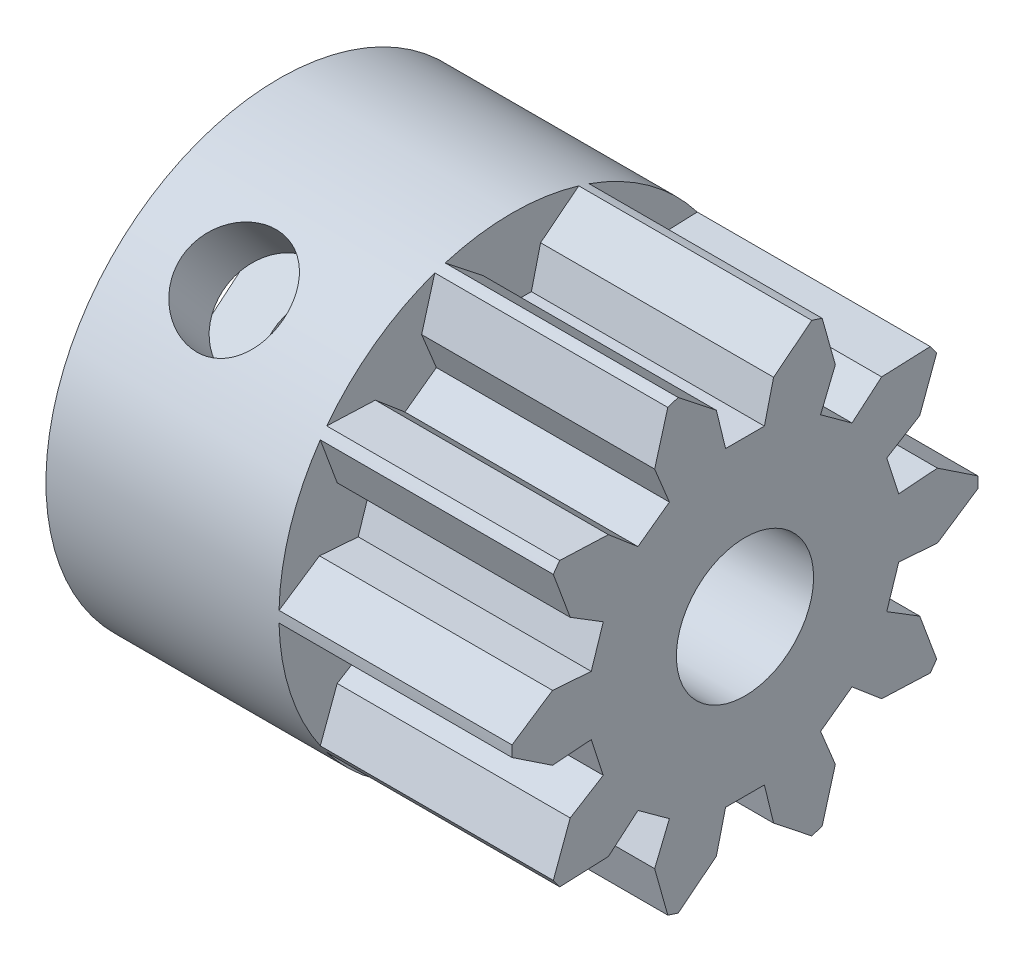
SolidWorks part; units mm, degrees
ref_plane "Plan de face" through (0, 0, 0) normal (0, 0, 1) x (1, 0, 0)
ref_plane "Plan de dessus" through (0, 0, 0) normal (0, 1, 0) x (1, 0, 0)
ref_plane "Plan de droite" through (0, 0, 0) normal (1, 0, 0) x (0, 0, -1)
sketch "Esquisse1" plane through (0, 0, 0) normal (1, 0, 0) x (0, 0, -1)
  circle A0 centre (0, 0) radius 9
  circle A1 centre (0, 0) radius 2.65
  dimension "D1" = 18
  dimension "D2" = 5.3
extrude "Boss.-Extru.1" add sketch "Esquisse1" along normal blind 18
sketch "Esquisse5" plane through (18, 0, 0) normal (1, 0, 0) x (0, 0, -1)
  line L0 (-0.75, 6) -> (0.75, 6)
  line L1 (0, 0) -> (0, 9) construction
  line L2 (-1.105, 7.4574) -> (1.105, 7.4574) construction
  line L3 (2.5796, 8.6224) -> (-2.5796, 8.6224) construction
  line L4 (-0.75, 6) -> (-1.105, 7.4574)
  line L5 (-1.105, 7.4574) -> (-2.5796, 8.6224)
  line L6 (0.75, 6) -> (1.105, 7.4574)
  line L7 (1.105, 7.4574) -> (2.5796, 8.6224)
  circle A0 centre (0, 0) radius 9 construction
  arc A1 (-2.5796, 8.6224) -> (2.5796, 8.6224) centre (0, 0) cw
  point P8 (0, 6)
  dimension "D1" = 1.5
  dimension "D2" = 3
  dimension "D3" = 1.5
  dimension "D4" = 142
  dimension "D5" = 2.21
extrude "Enlèv. mat.-Extru.2" cut sketch "Esquisse5" against normal blind 9
pattern_circular "Répétition circulaire1" count 10 over 360 about axis through (0, 0, 0) along (1, 0, 0) of "Enlèv. mat.-Extru.2"
sketch "Esquisse6" plane through (0, 0, 0) normal (-1, 0, 0) x (0, 0, 1)
  line L0 (-9, 0) -> (0, 0) construction
  line L2 (-6.5, 3) -> (-3.5, 3)
  line L3 (-6.5, 3) -> (-6.5, -3)
  line L4 (-6.5, -3) -> (-3.5, -3)
  line L5 (-3.5, 3) -> (-3.5, -3)
  line L6 (-6.5, 3) -> (-3.5, -3) construction
  line L7 (-6.5, -3) -> (-3.5, 3) construction
  circle A0 centre (0, 0) radius 9 construction
  point P5 (-5, 0)
  dimension "D1" = 6
  dimension "D2" = 3
  dimension "D3" = 2.5
extrude "Enlèv. mat.-Extru.3" cut sketch "Esquisse6" against normal blind 7
ref_plane "Plan1" through (0, 0, -9) normal (0, 0, -1) x (-1, 0, 0)
sketch "Esquisse7" plane through (0, 0, -9) normal (0, 0, -1) x (-1, 0, 0)
  line L0 (-4, 0) -> (0, 0) construction
  circle A0 centre (-4, 0) radius 2
  dimension "D2" = 4
  dimension "D1" = 4
extrude "Enlèv. mat.-Extru.4" cut sketch "Esquisse7" against normal blind 9
pattern_circular "Répétition circulaire2" count 2 over 130 about axis through (0, 0, 0) along (1, 0, 0) of "Enlèv. mat.-Extru.4", "Enlèv. mat.-Extru.3"
sketch "Esquisse8" plane through (18, 0, 0) normal (1, 0, 0) x (0, 0, -1)
  circle A0 centre (0, 0) radius 9
  dimension "D1" = 18
